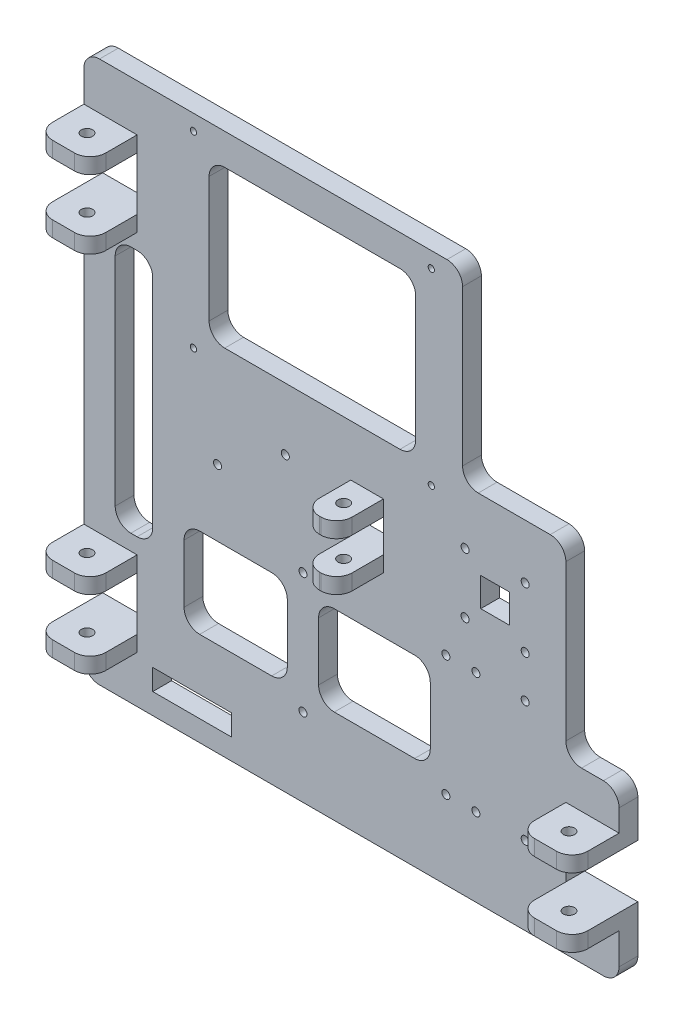
SolidWorks part; units mm, degrees
ref_plane "Front Plane" through (0, 0, 0) normal (0, 0, 1) x (1, 0, 0)
ref_plane "Top Plane" through (0, 0, 0) normal (0, 1, 0) x (1, 0, 0)
ref_plane "Right Plane" through (0, 0, 0) normal (1, 0, 0) x (0, 0, -1)
sketch "Sketch1" plane through (0, 0, 0) normal (0, 0, 1) x (-1, 0, 0)
  line L0 (0, -67.7412) -> (0, -193.7354)
  line L1 (0, -193.7354) -> (-21.59, -193.7354)
  line L2 (-21.59, -193.7354) -> (-21.59, -215.3254)
  line L3 (-21.59, -215.3254) -> (0, -215.3254)
  line L4 (0, -215.3254) -> (0, -240.7254)
  line L5 (0, -240.7254) -> (-153.67, -240.7254)
  line L6 (-121.56, -137.3726) -> (-121.56, -124.1039)
  line L7 (-108.2913, -130.7383) -> (0, -130.7383) construction
  line L8 (0, -20.7512) -> (0, 0) construction
  line L10 (-153.67, -165.0283) -> (-195.58, -165.0283)
  line L11 (-195.58, -165.0283) -> (-195.58, -89.3312)
  line L12 (-195.58, -89.3312) -> (-217.17, -89.3312)
  line L13 (-121.56, -137.3726) -> (-108.2913, -137.3726)
  line L14 (-108.2913, -137.3726) -> (-108.2913, -124.1039)
  line L16 (-121.56, -124.1039) -> (-108.2913, -124.1039)
  line L17 (0, -67.7412) -> (-21.59, -67.7412)
  line L18 (-21.59, -67.7412) -> (-21.59, -46.1512)
  line L19 (-21.59, -46.1512) -> (0, -46.1512)
  line L20 (0, -46.1512) -> (0, -20.7512)
  line L21 (0, -20.7512) -> (-217.17, -20.7512)
  line L22 (-217.17, -67.7412) -> (-195.58, -67.7412)
  line L23 (-195.58, -67.7412) -> (-195.58, -46.1512)
  line L24 (-195.58, -46.1512) -> (-217.17, -46.1512)
  line L25 (-153.67, -240.7254) -> (-153.67, -165.0283)
  line L26 (-217.17, -89.3312) -> (-217.17, -67.7412)
  line L27 (-217.17, -46.1512) -> (-217.17, -20.7512)
  line L30 (-21.59, -215.3254) -> (0, -215.3254)
  line L33 (-21.59, -193.7354) -> (-21.59, -215.3254)
  line L34 (0, -193.7354) -> (-21.59, -193.7354)
  point P36 (0, -130.7383)
  dimension "D1" = 21.59
  dimension "D2" = 217.17
  dimension "D3" = 25.4
  dimension "D4" = 125.9942
  dimension "D5" = 21.59
  dimension "D6" = 63.5
extrude "Boss-Extrude1" add sketch "Sketch1" along normal blind 7.62 contours L4 L5 L25 L10 L11 L12 L26 L22 L23 L24 L27 L21 L20 L19 L18 L17 L0 L1 L2 L3 | L14 L16 L6 L13
sketch "Sketch5" plane through (0, 0, 7.62) normal (0, 0, 1) x (1, 0, 0)
  line L0 (44.45, 196.2754) -> (140.97, 196.2754) construction
  line L1 (140.97, 158.1754) -> (44.45, 158.1754) construction
  line L2 (140.97, 158.1754) -> (140.97, 234.3754) construction
  line L3 (140.97, 234.3754) -> (44.45, 234.3754) construction
  line L4 (44.45, 158.1754) -> (44.45, 234.3754) construction
  line L5 (140.97, 158.1754) -> (44.45, 234.3754) construction
  line L6 (140.97, 234.3754) -> (44.45, 158.1754) construction
  line L7 (92.71, 158.1754) -> (92.71, 234.3754) construction
  line L8 (0, 240.7254) -> (153.67, 240.7254) construction
  line L9 (0, 215.3254) -> (0, 240.7254) construction
  circle A0 centre (44.45, 234.3754) radius 1.27
  circle A1 centre (140.97, 234.3754) radius 1.27
  circle A2 centre (44.45, 158.1754) radius 1.27
  circle A3 centre (140.97, 158.1754) radius 1.27
  point P0 (92.71, 196.2754)
  dimension "D3" = 2.54
  dimension "D1" = 76.2
  dimension "D2" = 6.35
  dimension "D4" = 44.45
  dimension "D5" = 96.52
extrude "Cut-Extrude3" cut sketch "Sketch5" against normal through all
sketch "Sketch8" plane through (0, 0, 0) normal (0, 0, -1) x (-1, 0, 0)
  line L0 (0, 20.7512) -> (-217.17, 20.7512) construction
  line L1 (-88.9, 101.5012) -> (-146.9, 101.5012) construction
  line L2 (-88.9, 101.5012) -> (-88.9, 52.5012) construction
  line L3 (0, 67.7412) -> (0, 193.7354) construction
  line L4 (-88.9, 52.5012) -> (-146.9, 52.5012) construction
  line L5 (-146.9, 101.5012) -> (-146.9, 52.5012) construction
  line L6 (-88.9, 101.5012) -> (-146.9, 52.5012) construction
  line L7 (-88.9, 52.5012) -> (-146.9, 101.5012) construction
  circle A0 centre (-88.9, 52.5012) radius 1.625
  circle A1 centre (-146.9, 52.5012) radius 1.625
  circle A2 centre (-88.9, 101.5012) radius 1.625
  circle A3 centre (-146.9, 101.5012) radius 1.625
  point P10 (-117.9, 77.0012)
  dimension "D5" = 3.25
  dimension "D1" = 58
  dimension "D2" = 49
  dimension "D3" = 31.75
  dimension "D4" = 88.9
sketch "Sketch9" plane through (0, 0, 0) normal (0, 0, -1) x (-1, 0, 0)
  line L1 (-27.94, 29.2177) -> (-59.94, 29.2177)
  line L2 (-27.94, 29.2177) -> (-27.94, 37.7177)
  line L3 (-27.94, 37.7177) -> (-59.94, 37.7177)
  line L4 (-59.94, 29.2177) -> (-59.94, 37.7177)
  line L6 (0, 20.7512) -> (-217.17, 20.7512) construction
  line L7 (-21.59, 67.7412) -> (-21.59, 46.1512) construction
  dimension "D1" = 8.4666
  dimension "D2" = 6.35
  dimension "D3" = 32
  dimension "D4" = 8.5
extrude "Cut-Extrude5" cut sketch "Sketch9" against normal up to next
sketch "Sketch10" plane through (0, 0, 7.62) normal (0, 0, 1) x (1, 0, 0)
  line L0 (179.07, 130.7383) -> (121.56, 130.7383) construction
  line L1 (154.686, 142.9303) -> (179.07, 142.9303) construction
  line L2 (154.686, 142.9303) -> (154.686, 118.5463) construction
  line L3 (154.686, 118.5463) -> (179.07, 118.5463) construction
  line L4 (179.07, 142.9303) -> (179.07, 118.5463) construction
  line L5 (154.686, 142.9303) -> (179.07, 118.5463) construction
  line L6 (154.686, 118.5463) -> (179.07, 142.9303) construction
  line L8 (217.17, 89.3312) -> (217.17, 67.7412) construction
  line L10 (121.56, 137.3726) -> (121.56, 124.1039) construction
  circle A0 centre (179.07, 142.9303) radius 1.625
  circle A1 centre (179.07, 118.5463) radius 1.625
  circle A2 centre (154.686, 118.5463) radius 1.625
  circle A3 centre (154.686, 142.9303) radius 1.625
  point P0 (166.878, 130.7383)
  dimension "D1" = 3.25
  dimension "D2" = 24.384
  dimension "D3" = 38.1
extrude "Cut-Extrude6" cut sketch "Sketch10" against normal through all
sketch "Sketch13" plane through (0, 0, 7.62) normal (0, 0, 1) x (1, 0, 0)
  line L0 (21.59, 67.7412) -> (21.59, 46.1512) construction
  line L1 (0, 215.3254) -> (21.59, 215.3254)
  line L2 (0, 215.3254) -> (0, 221.6754)
  line L3 (0, 221.6754) -> (21.59, 221.6754)
  line L4 (21.59, 215.3254) -> (21.59, 221.6754)
  line L5 (0, 193.7354) -> (21.59, 193.7354)
  line L6 (0, 193.7354) -> (0, 187.3854)
  line L7 (0, 187.3854) -> (21.59, 187.3854)
  line L8 (21.59, 193.7354) -> (21.59, 187.3854)
  line L9 (0, 46.1512) -> (21.59, 46.1512)
  line L10 (0, 46.1512) -> (0, 39.8012)
  line L11 (0, 39.8012) -> (21.59, 39.8012)
  line L12 (21.59, 46.1512) -> (21.59, 39.8012)
  line L13 (0, 67.7412) -> (21.59, 67.7412)
  line L14 (0, 67.7412) -> (0, 74.0912)
  line L15 (0, 74.0912) -> (21.59, 74.0912)
  line L16 (21.59, 67.7412) -> (21.59, 74.0912)
  line L17 (0, 67.7412) -> (21.59, 67.7412) construction
  line L18 (108.2913, 137.3726) -> (108.2913, 124.1039) construction
  line L19 (121.56, 137.3726) -> (108.2913, 137.3726)
  line L20 (121.56, 137.3726) -> (121.56, 143.7226)
  line L21 (121.56, 143.7226) -> (108.2913, 143.7226)
  line L22 (108.2913, 137.3726) -> (108.2913, 143.7226)
  line L23 (121.56, 124.1039) -> (108.2913, 124.1039)
  line L24 (121.56, 124.1039) -> (121.56, 117.7539)
  line L25 (121.56, 117.7539) -> (108.2913, 117.7539)
  line L26 (108.2913, 124.1039) -> (108.2913, 117.7539)
  line L27 (121.56, 124.1039) -> (108.2913, 124.1039) construction
  line L41 (217.17, 46.1512) -> (195.58, 46.1512)
  line L42 (217.17, 46.1512) -> (217.17, 39.8012)
  line L43 (217.17, 39.8012) -> (195.58, 39.8012)
  line L44 (195.58, 46.1512) -> (195.58, 39.8012)
  line L46 (195.58, 67.7412) -> (195.58, 46.1512) construction
  line L48 (217.17, 67.7412) -> (195.58, 67.7412)
  line L49 (217.17, 67.7412) -> (217.17, 74.0912)
  line L50 (217.17, 74.0912) -> (195.58, 74.0912)
  line L51 (195.58, 67.7412) -> (195.58, 74.0912)
  dimension "D1" = 6.35
extrude "Boss-Extrude2" add sketch "Sketch13" along normal blind 19.05
sketch "Sketch14" plane through (0, 39.8012, 0) normal (0, -1, 0) x (1, 0, 0)
  line L0 (10.795, 26.67) -> (10.795, 7.62) construction
  line L1 (0, 26.67) -> (21.59, 26.67) construction
  line L2 (0, 7.62) -> (21.59, 7.62) construction
  circle A0 centre (10.795, 17.145) radius 2.286
  dimension "D1" = 4.572
extrude "Cut-Extrude7" cut sketch "Sketch14" against normal through all
sketch "Sketch15" plane through (0, 117.7539, 0) normal (0, -1, 0) x (1, 0, 0)
  line L0 (114.9257, 26.67) -> (114.9257, 7.62) construction
  line L1 (108.2913, 26.67) -> (121.56, 26.67) construction
  line L2 (108.2913, 7.62) -> (121.56, 7.62) construction
  circle A0 centre (114.9257, 17.145) radius 2.286
  circle A1 centre (10.795, 17.145) radius 2.286 construction
extrude "Cut-Extrude8" cut sketch "Sketch15" against normal through all
extrude "Cut-Extrude9" cut sketch "Sketch8" against normal through all
sketch "Sketch19" plane through (0, 39.8012, 0) normal (0, -1, 0) x (1, 0, 0)
  line L0 (206.375, 7.62) -> (206.375, 26.67) construction
  line L1 (195.58, 7.62) -> (217.17, 7.62) construction
  line L2 (195.58, 26.67) -> (217.17, 26.67) construction
  circle A0 centre (206.375, 17.145) radius 2.286
  circle A1 centre (114.9257, 17.145) radius 2.286 construction
extrude "Cut-Extrude13" cut sketch "Sketch19" against normal through all
sketch "Sketch20" plane through (0, 0, 0) normal (0, 0, -1) x (-1, 0, 0)
  line L0 (-108.2913, 130.7383) -> (-24.1186, 130.7383) construction
  line L2 (-108.2913, 137.3726) -> (-108.2913, 124.1039) construction
  line L4 (-46.7413, 140.7383) -> (-89.2413, 140.7383) construction
  line L5 (-46.7413, 140.7383) -> (-46.7413, 120.7383) construction
  line L6 (-46.7413, 120.7383) -> (-89.2413, 120.7383) construction
  line L7 (-89.2413, 140.7383) -> (-89.2413, 120.7383) construction
  circle A0 centre (-81.7413, 139.3383) radius 1.625
  circle A1 centre (-54.2413, 122.1383) radius 1.625
  dimension "D4" = 3.25
  dimension "D9" = 3.25
  dimension "D1" = 10
  dimension "D2" = 20
  dimension "D3" = 7.5
  dimension "D5" = 19.05
  dimension "D6" = 42.5
  dimension "D7" = 7.5
  dimension "D8" = 2.8
  dimension "D10" = 2.8
extrude "Cut-Extrude14" cut sketch "Sketch20" against normal up to next
sketch "Sketch22" plane through (0, 0, 0) normal (0, 0, -1) x (-1, 0, 0)
  line L0 (-95.25, 77.0012) -> (-61.595, 77.0012) construction
  line L1 (-172.72, 136.5803) -> (-161.036, 136.5803)
  line L2 (-172.72, 136.5803) -> (-172.72, 124.8963)
  line L3 (-172.72, 124.8963) -> (-161.036, 124.8963)
  line L4 (-161.036, 136.5803) -> (-161.036, 124.8963)
  line L5 (-140.55, 95.1512) -> (-95.25, 95.1512)
  line L6 (-140.55, 95.1512) -> (-140.55, 58.8512)
  line L7 (-140.55, 58.8512) -> (-95.25, 58.8512)
  line L8 (-95.25, 95.1512) -> (-95.25, 58.8512)
  line L9 (-134.62, 228.0254) -> (-50.8, 228.0254)
  line L10 (-134.62, 228.0254) -> (-134.62, 164.5254)
  line L11 (-134.62, 164.5254) -> (-50.8, 164.5254)
  line L12 (-50.8, 228.0254) -> (-50.8, 164.5254)
  line L13 (-21.59, 67.7412) -> (-21.59, 46.1512) construction
  line L14 (-40.64, 58.8512) -> (-82.55, 58.8512)
  line L15 (-40.64, 58.8512) -> (-40.64, 95.1512)
  line L16 (-40.64, 95.1512) -> (-82.55, 95.1512)
  line L17 (-82.55, 58.8512) -> (-82.55, 95.1512)
  line L18 (-40.64, 58.8512) -> (-82.55, 95.1512) construction
  line L19 (-40.64, 95.1512) -> (-82.55, 58.8512) construction
  line L20 (0, 67.7412) -> (-21.59, 67.7412) construction
  line L21 (-12.7, 80.4412) -> (-27.94, 80.4412)
  line L22 (-12.7, 80.4412) -> (-12.7, 181.0354)
  line L23 (-12.7, 181.0354) -> (-27.94, 181.0354)
  line L24 (-27.94, 80.4412) -> (-27.94, 181.0354)
  line L25 (-12.7, 80.4412) -> (-27.94, 181.0354) construction
  line L26 (-12.7, 181.0354) -> (-27.94, 80.4412) construction
  line L27 (0, 193.7354) -> (-21.59, 193.7354) construction
  line L28 (0, 67.7412) -> (0, 193.7354) construction
  circle A0 centre (-179.07, 142.9303) radius 1.625 construction
  circle A2 centre (-179.07, 118.5463) radius 1.625 construction
  circle A3 centre (-154.686, 118.5463) radius 1.625 construction
  circle A4 centre (-154.686, 142.9303) radius 1.625 construction
  circle A5 centre (-146.9, 52.5012) radius 1.625 construction
  circle A6 centre (-146.9, 101.5012) radius 1.625 construction
  circle A7 centre (-88.9, 52.5012) radius 1.625 construction
  circle A8 centre (-140.97, 158.1754) radius 1.27 construction
  circle A9 centre (-44.45, 158.1754) radius 1.27 construction
  circle A10 centre (-44.45, 234.3754) radius 1.27 construction
  circle A11 centre (-88.9, 101.5012) radius 1.625 construction
  point P42 (-20.32, 130.7383)
  dimension "D1" = 6.35
  dimension "D6" = 6.35
  dimension "D11" = 6.35
  dimension "D2" = 6.35
  dimension "D3" = 6.35
  dimension "D4" = 6.35
  dimension "D5" = 6.35
  dimension "D7" = 6.35
  dimension "D8" = 6.35
  dimension "D9" = 6.35
  dimension "D10" = 6.35
  dimension "D12" = 6.35
  dimension "D13" = 6.35
  dimension "D14" = 19.05
  dimension "D15" = 12.7
  dimension "D16" = 12.7
  dimension "D17" = 12.7
  dimension "D18" = 12.7
extrude "Cut-Extrude15" cut sketch "Sketch22" against normal through all
sketch "Sketch24" plane through (0, 0, 0) normal (0, 0, -1) x (-1, 0, 0)
  line L0 (-159.07, 101.5012) -> (-146.9, 101.5012) construction
  line L1 (-179.07, 101.5012) -> (-159.07, 101.5012) construction
  line L2 (-179.07, 101.5012) -> (-179.07, 52.5012) construction
  line L3 (-179.07, 52.5012) -> (-159.07, 52.5012) construction
  line L4 (-159.07, 101.5012) -> (-159.07, 52.5012) construction
  line L5 (-179.07, 101.5012) -> (-159.07, 52.5012) construction
  line L6 (-179.07, 52.5012) -> (-159.07, 101.5012) construction
  line L7 (-159.07, 52.5012) -> (-146.9, 52.5012) construction
  line L8 (-179.07, 118.5463) -> (-179.07, 101.5012) construction
  circle A0 centre (-179.07, 101.5012) radius 1.625
  circle A1 centre (-159.07, 101.5012) radius 1.625
  circle A2 centre (-159.07, 52.5012) radius 1.625
  circle A3 centre (-179.07, 52.5012) radius 1.625
  circle A4 centre (-179.07, 118.5463) radius 1.625 construction
  point P0 (-169.07, 77.0012)
  dimension "D1" = 20
extrude "Cut-Extrude16" cut sketch "Sketch24" against normal through all
fillet "Fillet2" radius 6.35 16 edges at (0, 70.9162, 26.67) (21.59, 70.9162, 26.67) (21.59, 42.9762, 26.67) (0, 42.9762, 26.67) (0, 190.5604, 26.67) (21.59, 190.5604, 26.67) (21.59, 218.5004, 26.67) (0, 218.5004, 26.67) (121.56, 140.5476, 26.67) (108.2913, 140.5476, 26.67) (108.2913, 120.9289, 26.67) (121.56, 120.9289, 26.67) (195.58, 42.9762, 26.67) (217.17, 42.9762, 26.67) (195.58, 70.9162, 26.67) (217.17, 70.9162, 26.67)
fillet "Fillet4" radius 6.35 8 edges at (0, 20.7512, 3.81) (0, 240.7254, 3.81) (153.67, 240.7254, 3.81) (153.67, 165.0283, 3.81) (195.58, 165.0283, 3.81) (195.58, 89.3312, 3.81) (217.17, 20.7512, 3.81) (217.17, 89.3312, 3.81)
fillet "Fillet5" radius 6.35 16 edges at (140.55, 58.8512, 3.81) (95.25, 58.8512, 3.81) (95.25, 95.1512, 3.81) (140.55, 95.1512, 3.81) (134.62, 164.5254, 3.81) (50.8, 164.5254, 3.81) (50.8, 228.0254, 3.81) (134.62, 228.0254, 3.81) (82.55, 58.8512, 3.81) (40.64, 58.8512, 3.81) (40.64, 95.1512, 3.81) (82.55, 95.1512, 3.81) (12.7, 181.0354, 3.81) (27.94, 181.0354, 3.81) (27.94, 80.4412, 3.81) (12.7, 80.4412, 3.81)
